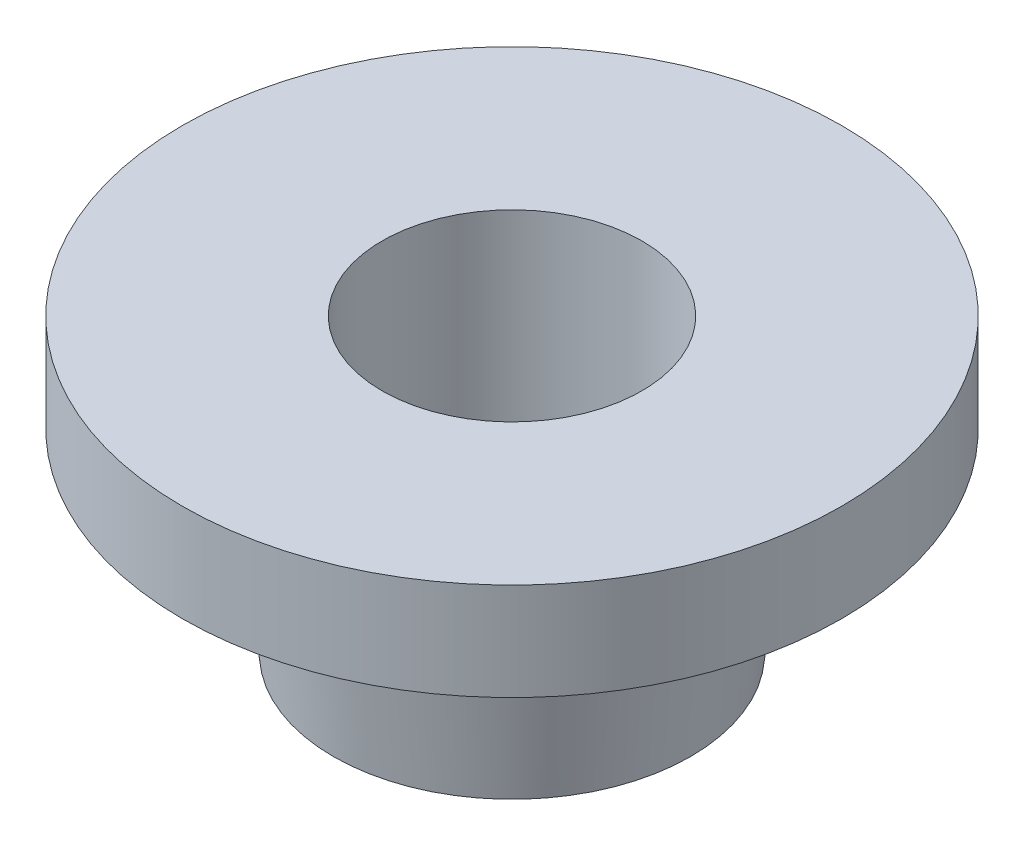
SolidWorks part; units mm, degrees
ref_plane "Front Plane" through (0, 0, 0) normal (0, 0, 1) x (1, 0, 0)
ref_plane "Top Plane" through (0, 0, 0) normal (0, 1, 0) x (1, 0, 0)
ref_plane "Right Plane" through (0, 0, 0) normal (1, 0, 0) x (0, 0, -1)
sketch "Sketch1" plane through (0, 0, 0) normal (0, 0, 1) x (1, 0, 0)
  line L1 (-4, 9) -> (-10.15, 9)
  line L2 (-10.15, 9) -> (-10.15, 6)
  line L3 (-10.15, 6) -> (-6.15, 6)
  line L4 (-6.15, 6) -> (-5.5, 0)
  line L5 (-5.5, 0) -> (-4, 0)
  line L6 (0, 0) -> (0, 9) construction
  line L8 (-4, 9) -> (-4, 0)
  point P2 (0, 0)
  point P8 (0, 0)
  point P10 (0, 0)
  dimension "D1" = 8
  dimension "D2" = 11
  dimension "D3" = 12.3
  dimension "D4" = 6
  dimension "D5" = 3
  dimension "D6" = 4
revolve "Revolve1" add sketch "Sketch1" angle 360 about L6
